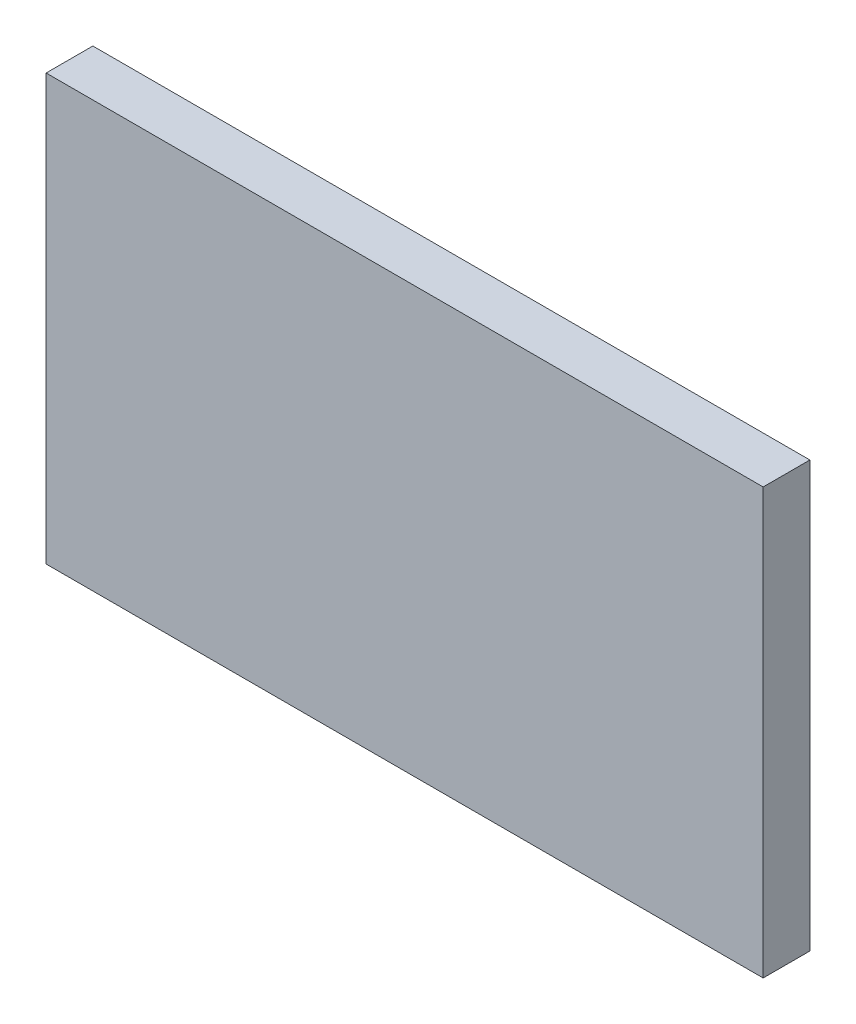
SolidWorks part; units mm, degrees
ref_plane "Front Plane" through (0, 0, 0) normal (0, 0, 1) x (1, 0, 0)
ref_plane "Top Plane" through (0, 0, 0) normal (0, 1, 0) x (1, 0, 0)
ref_plane "Right Plane" through (0, 0, 0) normal (1, 0, 0) x (0, 0, -1)
sketch "Sketch2" plane through (0, 0, 0) normal (0, 0, -1) x (-1, 0, 0)
  line L0 (222.9957, -9.5) -> (222.9957, -55)
  line L1 (222.9957, -9.5) -> (146.2775, -9.5)
  line L2 (222.9957, -55) -> (146.2775, -55)
  line L3 (146.2775, -9.5) -> (146.2775, -55)
  point P7 (0, 0)
  point P8 (147.9572, -5)
  dimension "D1" = 45.5
  dimension "D2" = 76.7182
extrude "Boss-Extrude1" add sketch "Sketch2" along normal blind 5
